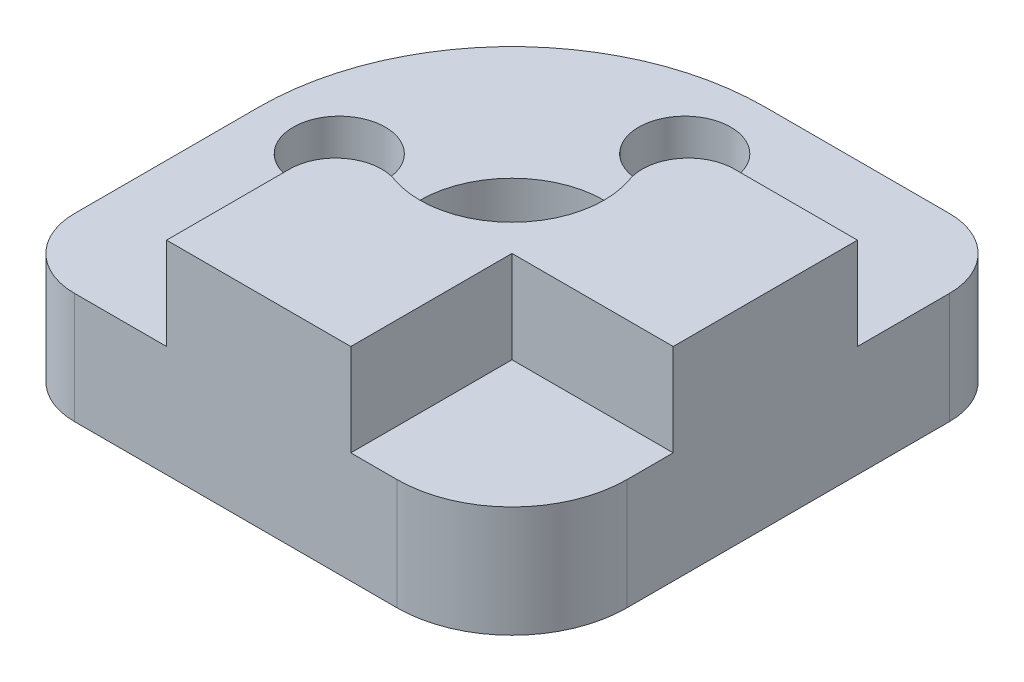
SolidWorks part; units mm, degrees
ref_plane "Front Plane" through (0, 0, 0) normal (0, 0, 1) x (1, 0, 0)
ref_plane "Top Plane" through (0, 0, 0) normal (0, 1, 0) x (1, 0, 0)
ref_plane "Right Plane" through (0, 0, 0) normal (1, 0, 0) x (0, 0, -1)
sketch "Sketch1" plane through (0, 0, 0) normal (0, 1, 0) x (1, 0, 0)
  line L0 (-11, 0) -> (-11, -8)
  line L1 (6, -11) -> (-8, -11)
  line L2 (11, -6) -> (11, 8)
  line L3 (0, 11) -> (8, 11)
  circle A0 centre (0, 0) radius 4
  circle A1 centre (-7.5, 0) radius 2
  circle A2 centre (0, 7.5) radius 2
  arc A3 (11, -6) -> (6, -11) centre (6, -6) cw
  arc A4 (11, 8) -> (8, 11) centre (8, 8) ccw
  arc A5 (-8, -11) -> (-11, -8) centre (-8, -8) cw
  arc A6 (0, 11) -> (-11, 0) centre (0, 0) ccw
  point P17 (-13, 13)
  dimension "D1" = 8
  dimension "D4" = 4
  dimension "D5" = 11
  dimension "D11" = 5
  dimension "D12" = 22
  dimension "D6" = 3
  dimension "D2" = 7.5
  dimension "D3" = 7.5
  dimension "D10" = 11
extrude "Boss-Extrude1" add sketch "Sketch1" along normal blind 4.825
sketch "Sketch2" plane through (0, 4.825, 0) normal (0, 1, 0) x (1, 0, 0)
  line L0 (4, -11) -> (4, -4)
  line L1 (4, -4) -> (11, -4)
  line L2 (5.6569, 4) -> (11, 4)
  line L3 (-4, -5.6569) -> (-4, -11)
  line L4 (-8, -11) -> (6, -11) construction
  line L5 (11, -6) -> (11, 8) construction
  line L6 (-4, -11) -> (4, -11)
  line L7 (11, -4) -> (11, 4)
  circle A0 centre (0, 0) radius 4 construction
  arc A1 (-1.3333, -3.7712) -> (3.7712, 1.3333) centre (0, 0) ccw
  arc A5 (3.7712, 1.3333) -> (5.6569, 4) centre (5.6569, 2) cw
  arc A6 (-1.3333, -3.7712) -> (-4, -5.6569) centre (-2, -5.6569) ccw
  dimension "D5" = 2
  dimension "D1" = 4
  dimension "D2" = 4
  dimension "D3" = 8
  dimension "D4" = 8
extrude "Boss-Extrude2" add sketch "Sketch2" along normal blind 4
